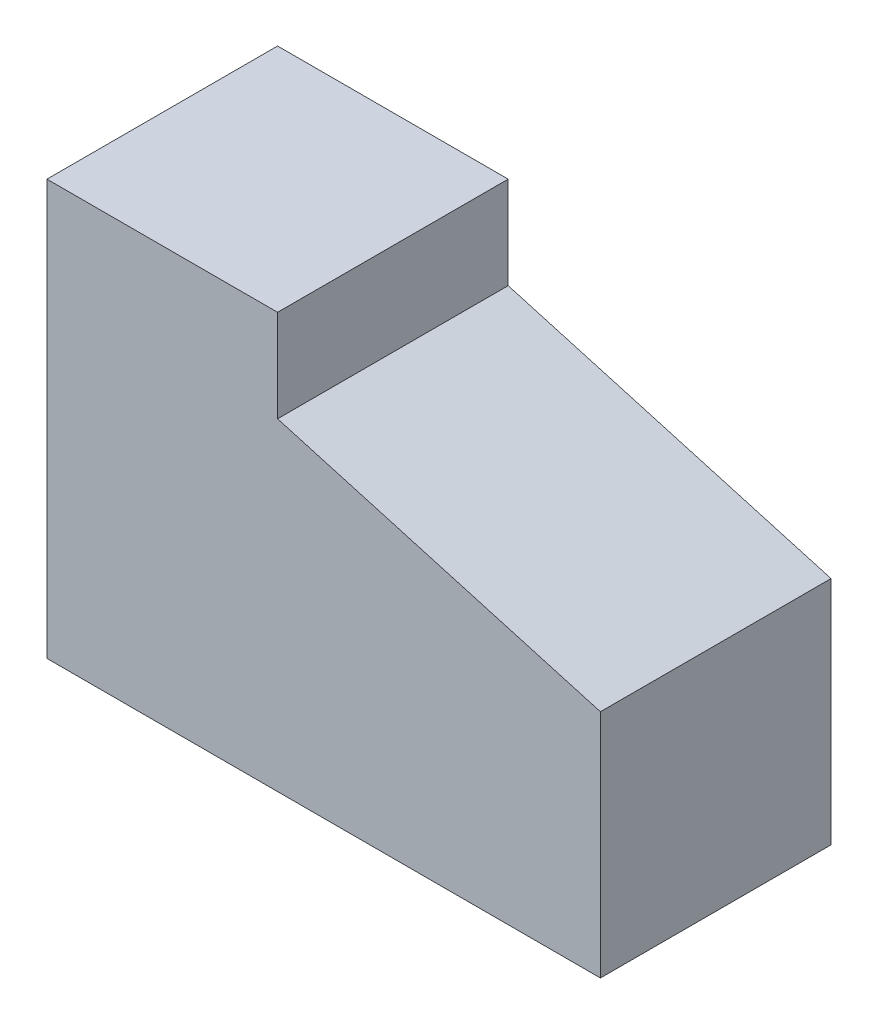
SolidWorks part; units mm, degrees
ref_plane "Front Plane" through (0, 0, 0) normal (0, 0, 1) x (1, 0, 0)
ref_plane "Top Plane" through (0, 0, 0) normal (0, 1, 0) x (1, 0, 0)
ref_plane "Right Plane" through (0, 0, 0) normal (1, 0, 0) x (0, 0, -1)
sketch "Sketch1" plane through (0, 0, 0) normal (0, 0, 1) x (1, 0, 0)
  line L0 (127, 228.6) -> (127, 177.8)
  line L1 (0, 0) -> (304.8, 0)
  line L2 (0, 0) -> (0, 228.6)
  line L3 (0, 228.6) -> (127, 228.6)
  line L4 (304.8, 0) -> (304.8, 127)
  line L5 (127, 177.8) -> (304.8, 127)
  dimension "D1" = 304.8
  dimension "D2" = 228.6
  dimension "D3" = 127
  dimension "D4" = 50.8
  dimension "D5" = 127
extrude "Boss-Extrude1" add sketch "Sketch1" along normal blind 127
